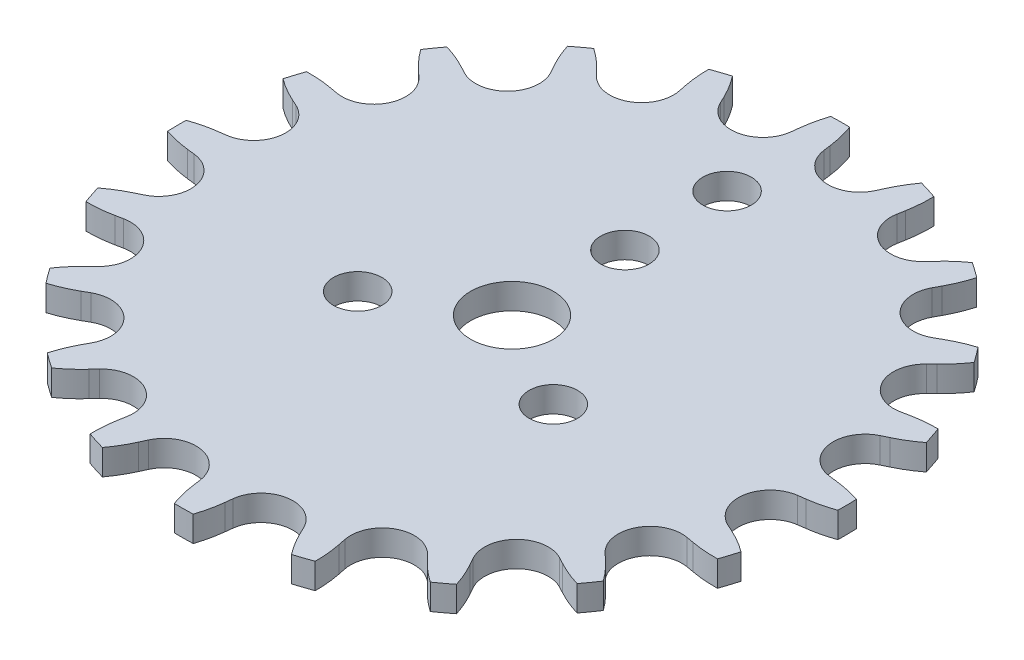
SolidWorks part; units mm, degrees
material "1060 Alloy"
ref_plane "Front Plane" through (0, 0, 0) normal (0, 0, 1) x (1, 0, 0)
ref_plane "Top Plane" through (0, 0, 0) normal (0, 1, 0) x (1, 0, 0)
ref_plane "Right Plane" through (0, 0, 0) normal (1, 0, 0) x (0, 0, -1)
sketch "Sketch1" plane through (0, 0, 0) normal (0, 1, 0) x (1, 0, 0)
  circle A0 centre (0, 0) radius 26
  dimension "D1" = 52
extrude "Boss-Extrude1" add sketch "Sketch1" along normal blind 2
sketch "Sketch2" plane through (0, 2, 0) normal (0, 1, 0) x (1, 0, 0)
  line L0 (0, -26) -> (0, 26) construction
  line L1 (25.7961, -3.25) -> (-25.7961, -3.25)
  line L2 (0, 8.85) -> (-24.4474, 8.85) construction
  line L3 (0, 10.75) -> (-23.6736, 10.75) construction
  line L4 (0, 18.75) -> (-18.0121, 18.75) construction
  line L5 (-5, 9.5164) -> (5, 9.5164) construction
  circle A0 centre (0, 0) radius 3.25
  circle A1 centre (0, 0) radius 8.85
  circle A2 centre (0, 0) radius 26 construction
  circle A3 centre (0, 8.85) radius 1.9
  circle A4 centre (7.6643, -4.425) radius 1.9
  circle A5 centre (-7.6643, -4.425) radius 1.9
  circle A6 centre (0, 0) radius 10.75
  circle A7 centre (0, 0) radius 18.75
  circle A8 centre (0, 16.85) radius 1.9
  point P12 (0, -3.25)
  point P22 (0, 0)
  point P26 (-9.0061, 18.75)
  dimension "D1" = 6.5
  dimension "D2" = 12.1
  dimension "D3" = 3.8
  dimension "D5" = 8
  dimension "D6" = 10
  dimension "D4" = 3
extrude "Cut-Extrude1" cut sketch "Sketch2" against normal through all contours A0 | L1 A5 A1 | A1 A5 L1 | L1 A5 A1 | A1 A5 L1 | L1 A4 A1 | A1 A4 L1 | A1 A4 L1 | L1 A4 A1 | A1 A3 | A1 A3 | A8
sketch "Sketch4" plane through (0, 2, 0) normal (0, 1, 0) x (1, 0, 0)
  line L0 (0, 0) -> (0, 24) construction
  line L1 (0, 0) -> (-4, 23.6643)
  line L2 (0, 0) -> (4, 23.6643)
  line L3 (-1.4506, 23.9561) -> (-1.5161, 23.3813)
  line L4 (1.4506, 23.9561) -> (1.5161, 23.3813)
  line L5 (-6.5037, 23.102) -> (-6.2529, 22.5806)
  circle A0 centre (0, 0) radius 24
  circle A1 centre (0, 0) radius 26 construction
  circle A2 centre (-4, 23.6643) radius 2.5
  circle A3 centre (4, 23.6643) radius 2.5
  arc A4 (-1.4506, 23.9561) -> (-1.0036, 25.9806) centre (8.4851, 22.8241) cw
  arc A5 (1.4506, 23.9561) -> (1.0036, 25.9806) centre (-8.4851, 22.8241) ccw
  arc A6 (-6.5037, 23.102) -> (-7.5912, 24.8671) centre (-15.5154, 18.7673) ccw
  point P10 (1.0188, 25.0956)
  point P12 (-0.9999, 23.9792)
  point P18 (-0.9997, 23.9792)
  point P19 (0, 0)
  dimension "D1" = 2
  dimension "D3" = 5
  dimension "D5" = 10
  dimension "D2" = 8
  dimension "D4" = 13
sketch "Sketch5" plane through (0, 2, 0) normal (0, 1, 0) x (1, 0, 0)
  line L0 (-6.5037, 23.102) -> (-6.2529, 22.5806) construction
  line L1 (-1.4506, 23.9561) -> (-1.5161, 23.3813) construction
  line L2 (-6.5037, 23.102) -> (-6.2529, 22.5806)
  line L3 (-1.4506, 23.9561) -> (-1.5161, 23.3813)
  arc A0 (-1.0036, 25.9806) -> (-1.4506, 23.9561) centre (8.4851, 22.8241) ccw construction
  circle A1 centre (0, 0) radius 26
  circle A2 centre (0, 0) radius 26
  arc A3 (-6.5037, 23.102) -> (-7.5912, 24.8671) centre (-15.5154, 18.7673) ccw construction
  circle A4 centre (-4, 23.6643) radius 2.5 construction
  arc A5 (-1.0036, 25.9806) -> (-1.4506, 23.9561) centre (8.4851, 22.8241) ccw
  arc A6 (-6.5037, 23.102) -> (-7.5912, 24.8671) centre (-15.5154, 18.7673) ccw
  arc A7 (-6.2529, 22.5806) -> (-1.5161, 23.3813) centre (-4, 23.6643) ccw
  arc A8 (-7.5912, 24.8671) -> (-1.0036, 25.9806) centre (0, 0) cw
  circle M13 centre (0, 0) radius 26
  dimension "D1" = 0
extrude "Cut-Extrude2" cut sketch "Sketch5" against normal blind 10 contours L2 A7 L3 A5 A6 M13
pattern_circular "CirPattern1" count 20 over 360 about axis through (0, 0, 0) along (0, 1, 0) of "Cut-Extrude2"
